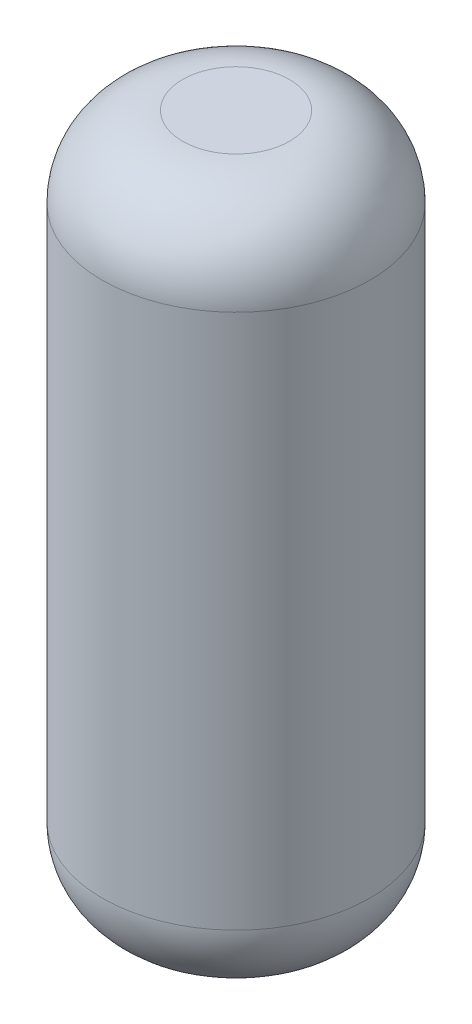
SolidWorks part; units mm, degrees
ref_plane "Alzado" through (0, 0, 0) normal (0, 0, 1) x (1, 0, 0)
ref_plane "Planta" through (0, 0, 0) normal (0, 1, 0) x (1, 0, 0)
ref_plane "Vista lateral" through (0, 0, 0) normal (1, 0, 0) x (0, 0, -1)
sketch "Croquis1" plane through (0, 0, 0) normal (0, 1, 0) x (1, 0, 0)
  circle A0 centre (0, 0) radius 5
  dimension "D1" = 10
extrude "Saliente-Extruir1" add sketch "Croquis1" along normal blind 26
fillet "Redondeo1" radius 3 2 edges at (0, 0, 5) (0, 26, 5)
